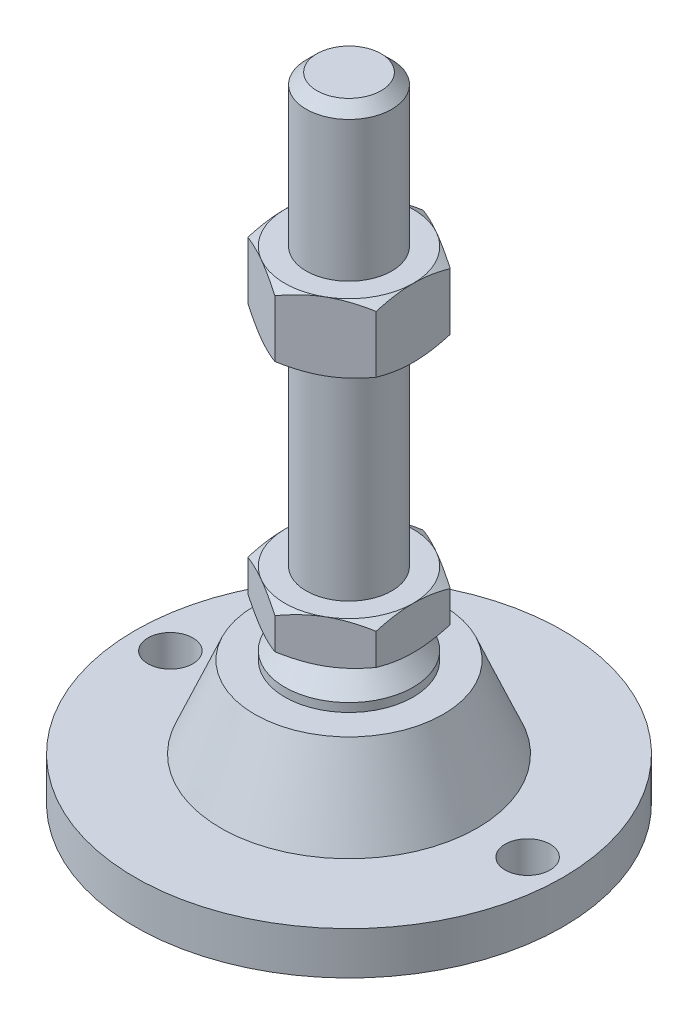
SolidWorks part; units mm, degrees
ref_plane "Спереди" through (0, 0, 0) normal (0, 0, 1) x (1, 0, 0)
ref_plane "Сверху" through (0, 0, 0) normal (0, 1, 0) x (1, 0, 0)
ref_plane "Справа" through (0, 0, 0) normal (1, 0, 0) x (0, 0, -1)
sketch "Эскиз1" plane through (0, 0, 0) normal (0, 0, 1) x (1, 0, 0)
  line L0 (0, 0) -> (-50, 0)
  line L3 (-50, 0) -> (-50, 10)
  line L12 (-10, 48) -> (-10, 145.5)
  line L13 (-10, 145.5) -> (-7.5, 148)
  line L14 (-7.5, 148) -> (0, 148)
  line L15 (0, 148) -> (0, 0) construction
  line L16 (-50, 10) -> (-30, 10)
  line L17 (0, 0) -> (0, 148)
  line L18 (0, 0) -> (0, -7.9595) construction
  line L19 (-10, 48) -> (-10, 38)
  line L21 (-15, 29) -> (-22, 29)
  line L22 (-30, 10) -> (-22, 29)
  line L23 (-15, 29) -> (-15, 31)
  line L24 (-15, 31) -> (-10, 36)
  line L25 (-10, 36) -> (-10, 38)
  line L26 (-10, 48) -> (0, 48) construction
  point P8 (-10, 96.75)
revolve "Повернуть1" add sketch "Эскиз1" angle 360 about L17
ref_plane "Плоскость2" through (0, 38, 0) normal (0, 1, 0) x (1, 0, 0)
sketch "Эскиз2" plane through (0, 38, 0) normal (0, 1, 0) x (1, 0, 0)
  line L1 (0, 17.3205) -> (-15, 8.6603)
  line L2 (-15, 8.6603) -> (-15, -8.6603)
  line L3 (-15, -8.6603) -> (0, -17.3205)
  line L4 (0, -17.3205) -> (15, -8.6603)
  line L5 (15, -8.6603) -> (15, 8.6603)
  line L6 (15, 8.6603) -> (0, 17.3205)
  circle A0 centre (0, 0) radius 15 construction
  dimension "D1" = 30
extrude "Бобышка-Вытянуть1" add sketch "Эскиз2" along normal up to vertex (10 mm away) up to point (-10, 48, 0)
ref_plane "Плоскость1" through (0, 96.75, 0) normal (0, 1, 0) x (1, 0, 0)
sketch "Эскиз3" plane through (0, 96.75, 0) normal (0, 1, 0) x (1, 0, 0)
  line L6 (15, 8.6603) -> (0, 17.3205)
  line L7 (0, 17.3205) -> (-15, 8.6603)
  line L8 (-15, 8.6603) -> (-15, -8.6603)
  line L9 (-15, -8.6603) -> (0, -17.3205)
  line L10 (0, -17.3205) -> (15, -8.6603)
  line L11 (15, -8.6603) -> (15, 8.6603)
  line L12 (15, 8.6603) -> (0, 17.3205)
  line L13 (0, 17.3205) -> (-15, 8.6603)
  line L14 (-15, 8.6603) -> (-15, -8.6603)
  line L15 (-15, -8.6603) -> (0, -17.3205)
  line L16 (0, -17.3205) -> (15, -8.6603)
  line L17 (15, -8.6603) -> (15, 8.6603)
  dimension "D1" = 0
extrude "Бобышка-Вытянуть2" add sketch "Эскиз3" along normal blind 16
sketch "Эскиз4" plane through (0, 0, 0) normal (0, 0, 1) x (1, 0, 0)
  line L0 (-15, 112.75) -> (-28.8564, 104.75)
  line L1 (-28.8564, 104.75) -> (-28.8564, 112.75)
  line L2 (-28.8564, 112.75) -> (-15, 112.75)
  line L3 (-28.8564, 104.75) -> (-15, 96.75)
  line L4 (50, 96.75) -> (-50, 96.75) construction
  line L5 (-15, 96.75) -> (-28.8564, 96.75)
  line L6 (-28.8564, 96.75) -> (-28.8564, 104.75)
  line L7 (-15, 112.75) -> (-15, 96.75) construction
  line L8 (-15, 48) -> (-23.6603, 48)
  line L9 (-23.6603, 48) -> (-23.6603, 43)
  line L10 (-23.6603, 43) -> (-15, 48)
  line L11 (-15, 38) -> (-23.6603, 43)
  line L12 (-23.6603, 43) -> (-23.6603, 38)
  line L13 (-23.6603, 38) -> (-15, 38)
  line L14 (0, 148) -> (0, 96.3793) construction
  line L15 (50, 38) -> (-50, 38) construction
  dimension "D1" = 30
  dimension "D2" = 30
revolve "Вырез-Повернуть2" cut sketch "Эскиз4" angle 360 about L14
sketch "Эскиз5" plane through (0, 10, 0) normal (0, 1, 0) x (1, 0, 0)
  line L0 (41.75, 0) -> (-41.75, 0) construction
  circle A0 centre (-41.75, 0) radius 5.25
  circle A1 centre (41.75, 0) radius 5.25
  circle A2 centre (0, 0) radius 50 construction
  dimension "D1" = 10.5
  dimension "D2" = 3
extrude "Вырез-Вытянуть1" cut sketch "Эскиз5" against normal through all
equation "\"D13@Эскиз1\"=\"D12@Эскиз1\"/2"
